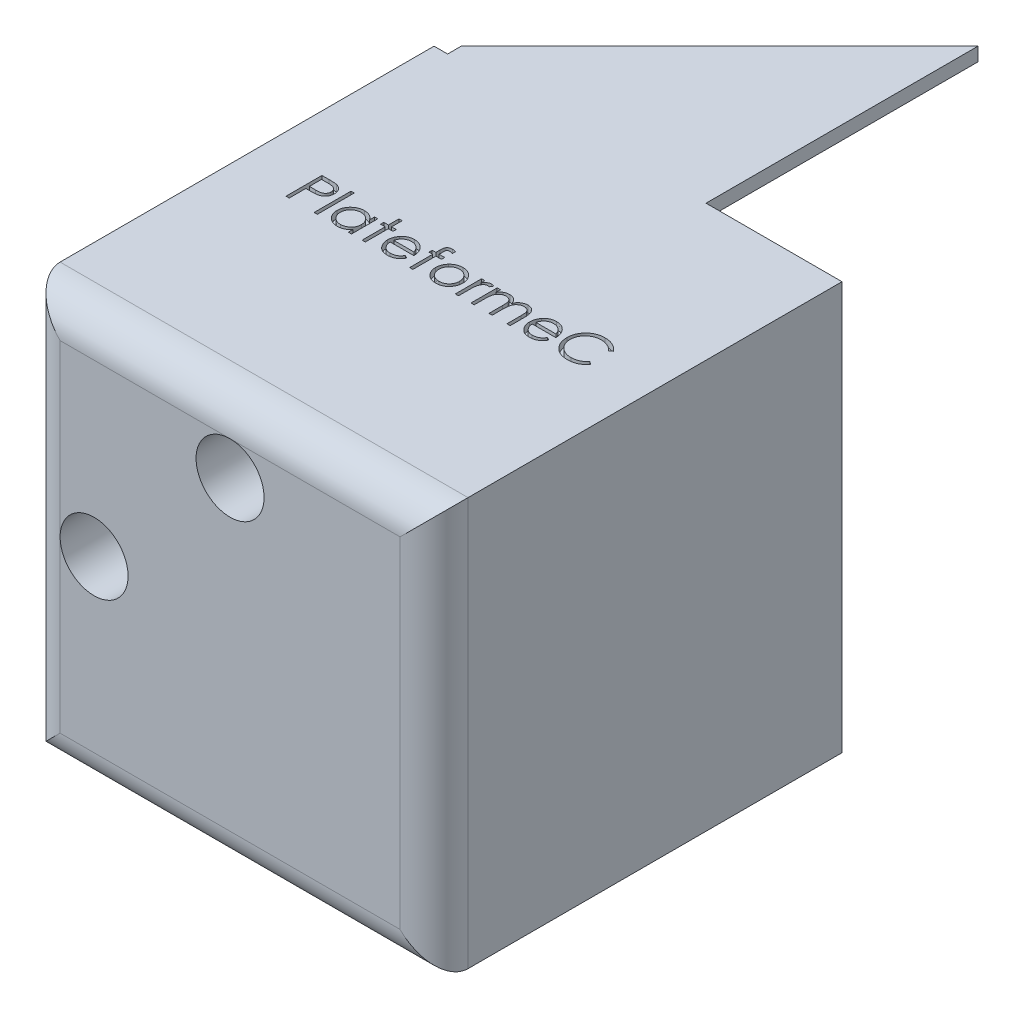
SolidWorks part; units mm, degrees
ref_plane "Plan de face" through (0, 0, 0) normal (0, 0, 1) x (1, 0, 0)
ref_plane "Plan de dessus" through (0, 0, 0) normal (0, 1, 0) x (1, 0, 0)
ref_plane "Plan de droite" through (0, 0, 0) normal (1, 0, 0) x (0, 0, -1)
sketch "Esquisse1" plane through (0, 0, 0) normal (0, 0, 1) x (1, 0, 0)
  line L1 (0, 0) -> (-60, 0)
  line L2 (0, 0) -> (0, 60)
  line L3 (0, 60) -> (-60, 60)
  line L4 (-60, 0) -> (-60, 60)
  dimension "D1" = 60
  dimension "D2" = 60
extrude "Boss.-Extru.1" add sketch "Esquisse1" along normal blind 60
sketch "Esquisse3" plane through (0, 0, 0) normal (0, 0, -1) x (-1, 0, 0)
  line L0 (60, 60) -> (60, 20)
  line L1 (60, 60) -> (60, 0) construction
  line L2 (60, 20) -> (58, 20)
  line L3 (58, 20) -> (58, 58)
  line L4 (58, 58) -> (20, 58)
  line L5 (20, 58) -> (20, 60)
  line L6 (0, 60) -> (60, 60) construction
  line L7 (20, 60) -> (60, 60)
  dimension "D1" = 40
  dimension "D2" = 40
  dimension "D3" = 2
  dimension "D4" = 2
extrude "Boss.-Extru.3" add sketch "Esquisse3" along normal blind 40
sketch "Esquisse6" plane through (-60, 0, 0) normal (-1, 0, 0) x (0, 0, 1)
  line L0 (30, 0) -> (30, 60) construction
  line L1 (60, 0) -> (0, 0) construction
  line L2 (60, 60) -> (-40, 60) construction
  text T0 "PING" font "Century Gothic" height in points 48
extrude "Enlèv. mat.-Extru.3" cut sketch "Esquisse6" against normal blind 1
sketch "Esquisse7" plane through (0, 60, 0) normal (0, 1, 0) x (1, 0, 0)
  line L0 (0, -30) -> (-60, -30) construction
  line L1 (0, -60) -> (0, 0) construction
  line L2 (-60, -60) -> (-60, 40) construction
  text T0 "PlateformeC" font "Century Gothic" height in points 20
extrude "Enlèv. mat.-Extru.4" cut sketch "Esquisse7" against normal blind 1
sketch "Esquisse8" plane through (-60, 0, 0) normal (-1, 0, 0) x (0, 0, 1)
  line L0 (-40, 20) -> (0, 60)
  line L1 (60, 60) -> (-40, 60) construction
  line L2 (0, 60) -> (-40, 60)
  line L3 (-40, 60) -> (-40, 20)
  dimension "D1" = 45
extrude "Enlèv. mat.-Extru.5" cut sketch "Esquisse8" against normal blind 2
sketch "Esquisse11" plane through (0, 60, 0) normal (0, 1, 0) x (1, 0, 0)
  line L0 (-20, 40) -> (-60, 0)
  line L1 (-60, 0) -> (-61.461, 41.461)
  line L2 (-61.461, 41.461) -> (-20, 40)
extrude "Enlèv. mat.-Extru.6" cut sketch "Esquisse11" against normal blind 2
fillet "Congé1" radius 5 4 edges at (-30, 0, 60) (0, 30, 60) (-60, 30, 60) (-30, 60, 60)
sketch "Esquisse13" plane through (0, 0, 60) normal (0, 0, 1) x (1, 0, 0)
  line L0 (-60, 60) -> (0, 60) construction
  line L1 (-60, 0) -> (-60, 60) construction
  circle A0 centre (-50, 30) radius 3
  circle A1 centre (-30, 50) radius 3
  dimension "D1" = 6
  dimension "D2" = 6
  dimension "D3" = 10
  dimension "D4" = 10
  dimension "D5" = 30
  dimension "D6" = 30
extrude "Enlèv. mat.-Extru.7" cut sketch "Esquisse13" against normal through all
sketch "Esquisse14" plane through (0, 0, 60) normal (0, 0, 1) x (1, 0, 0)
  circle A0 centre (-50, 30) radius 5
  circle A1 centre (-30, 50) radius 5
extrude "Enlèv. mat.-Extru.8" cut sketch "Esquisse14" against normal blind 54
